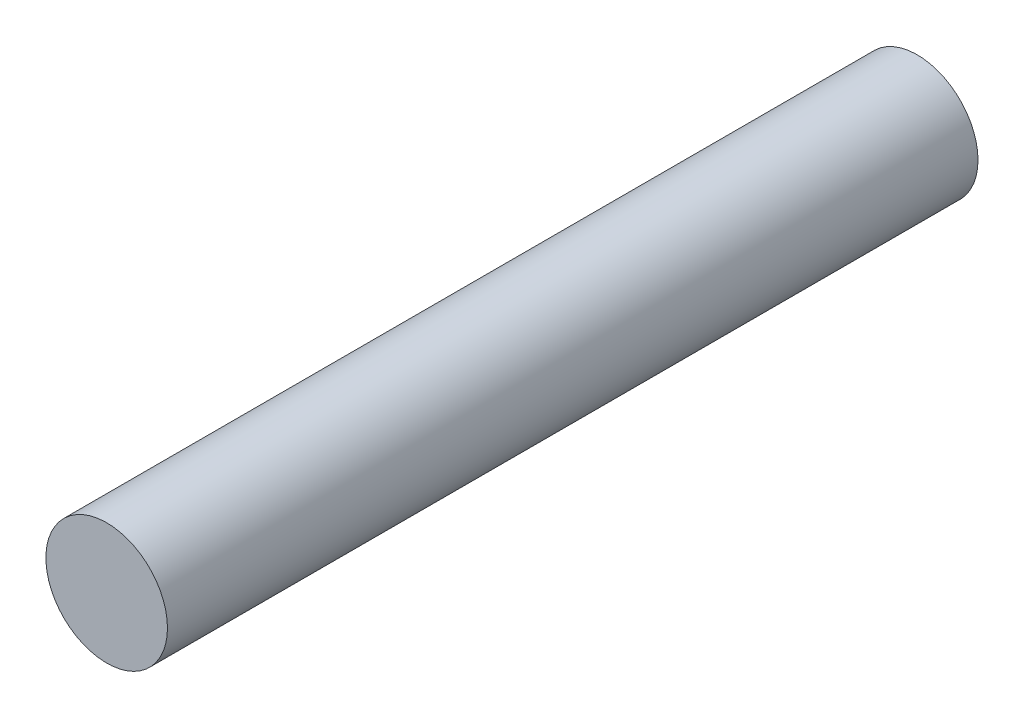
SolidWorks part; units mm, degrees
ref_plane "Alzado" through (0, 0, 0) normal (0, 0, 1) x (1, 0, 0)
ref_plane "Planta" through (0, 0, 0) normal (0, 1, 0) x (1, 0, 0)
ref_plane "Vista lateral" through (0, 0, 0) normal (1, 0, 0) x (0, 0, -1)
sketch "Croquis1" plane through (0, 0, 0) normal (0, 0, 1) x (1, 0, 0)
  circle A0 centre (0, 0) radius 7.5
  dimension "D1" = 15
extrude "Saliente-Extruir1" add sketch "Croquis1" along normal mid plane 100
